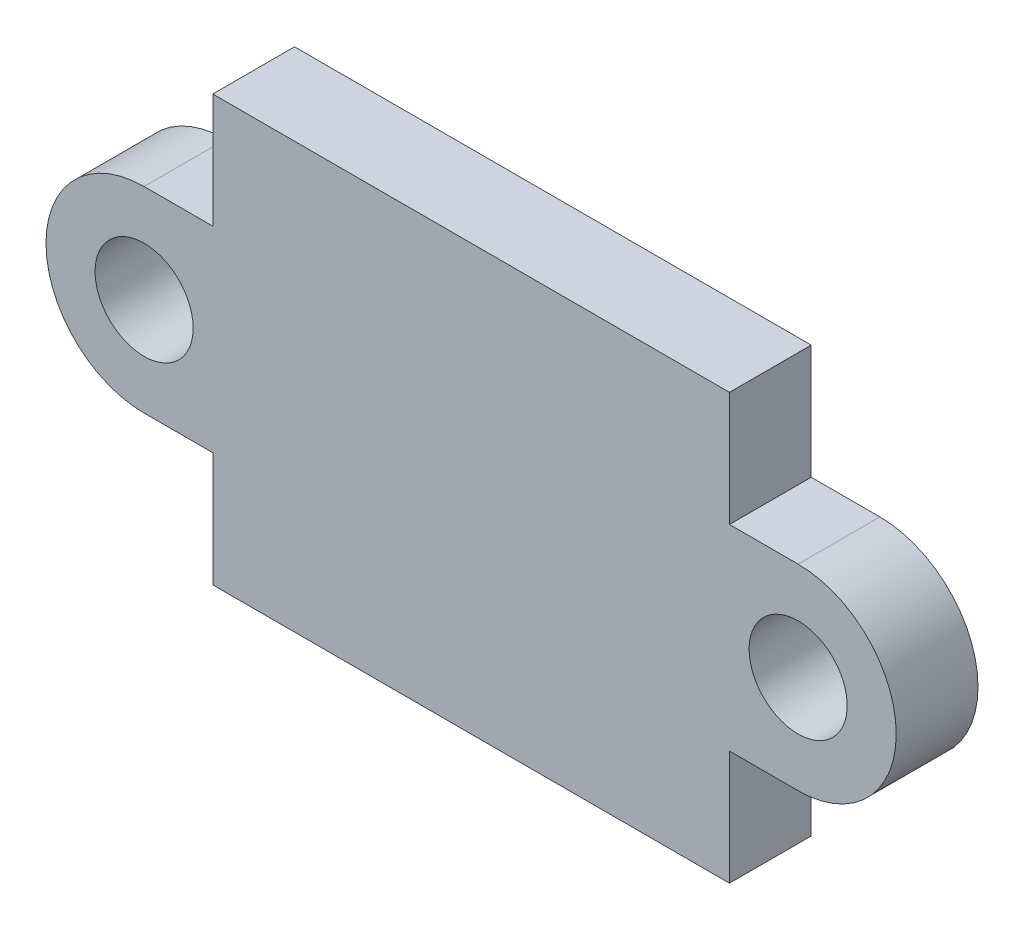
SolidWorks part; units mm, degrees
ref_plane "Plano frontal" through (0, 0, 0) normal (0, 0, 1) x (1, 0, 0)
ref_plane "Plano superior" through (0, 0, 0) normal (0, 1, 0) x (1, 0, 0)
ref_plane "Plano direito" through (0, 0, 0) normal (1, 0, 0) x (0, 0, -1)
sketch "Esboço1" plane through (0, 0, 0) normal (0, 0, 1) x (1, 0, 0)
  line L0 (-10, 3) -> (-7.9, 3)
  line L1 (-7.9, 3) -> (-7.9, 6.5)
  line L2 (-7.9, 6.5) -> (7.9, 6.5)
  line L3 (0, 0.6226) -> (0, -0.6226) construction
  line L4 (-10, -3) -> (-7.9, -3)
  line L5 (-7.9, -3) -> (-7.9, -6.5)
  line L6 (-7.9, -6.5) -> (7.9, -6.5)
  line L7 (7.9, -3) -> (7.9, -6.5)
  line L8 (10, -3) -> (7.9, -3)
  line L9 (7.9, 3) -> (7.9, 6.5)
  line L10 (10, 3) -> (7.9, 3)
  circle A0 centre (-10, 0) radius 1.5
  arc A1 (-10, 3) -> (-10, -3) centre (-10, 0) ccw
  arc A2 (10, 3) -> (10, -3) centre (10, 0) cw
  circle A3 centre (10, 0) radius 1.5
  point P2 (2.7976, -5.8774)
  point P8 (0, 0)
  point P9 (0, 0)
  point P21 (0, -6.5)
  point P23 (0, 6.5)
  dimension "D1" = 3
  dimension "D2" = 3
  dimension "D3" = 10
  dimension "D4" = 13
  dimension "D5" = 15.8
extrude "Ressalto-extrusão1" add sketch "Esboço1" along normal blind 2.5
